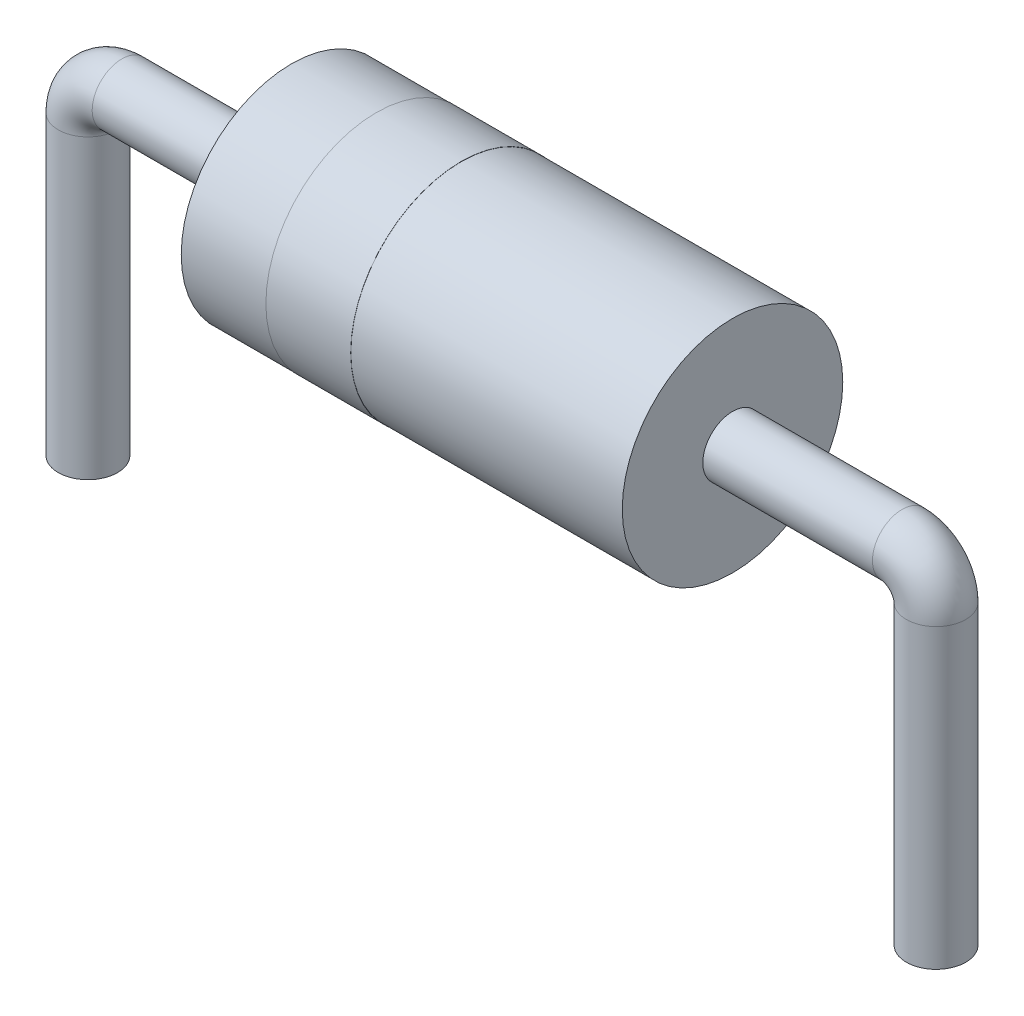
SolidWorks part; units mm, degrees
ref_plane "Ebene vorne" through (0, 0, 0) normal (0, 0, 1) x (1, 0, 0)
ref_plane "Ebene oben" through (0, 0, 0) normal (0, 1, 0) x (1, 0, 0)
ref_plane "Ebene rechts" through (0, 0, 0) normal (1, 0, 0) x (0, 0, -1)
sketch "Skizze1" plane through (0, 0, 0) normal (1, 0, 0) x (0, 0, -1)
  circle A0 centre (0, 0) radius 1.3
extrude "Aufsatz-Linear austragen1" add sketch "Skizze1" along normal blind 5.2
ref_plane "Ebene1" through (2, 0, 0) normal (-1, 0, 0) x (0, 0, 1)
sketch "Skizze4" plane through (2, 0, 0) normal (-1, 0, 0) x (0, 0, 1)
  circle A0 centre (0, 0) radius 1.302
extrude "Aufsatz-Linear austragen2" add sketch "Skizze4" along normal blind 1
sketch "Skizze10" plane through (5.2, 0, 0) normal (1, 0, 0) x (0, 0, -1)
  circle A0 centre (0, 0) radius 0.35
sketch "Skizze11" plane through (0, 0, 0) normal (0, 0, 1) x (1, 0, 0)
  line L0 (5.2, 0) -> (7.2, 0)
  line L1 (5.2, -0.35) -> (5.2, 0.35) construction
  line L2 (7.6, -0.4) -> (7.6, -3.9)
  arc A0 (7.2, 0) -> (7.6, -0.4) centre (7.2, -0.4) cw
sketch "Skizze12" plane through (0, 0, 0) normal (-1, 0, 0) x (0, 0, 1)
  circle A0 centre (0, 0) radius 0.35
sketch "Skizze13" plane through (0, 0, 0) normal (0, 0, 1) x (1, 0, 0)
  line L0 (0, 0) -> (-2, 0)
  line L1 (-2.4, -0.4) -> (-2.4, -3.9)
  arc A0 (-2, 0) -> (-2.4, -0.4) centre (-2, -0.4) ccw
sweep "Austragung3" add profiles "Skizze10" path "Skizze11"
sweep "Austragung4" add profiles "Skizze12" path "Skizze13"
